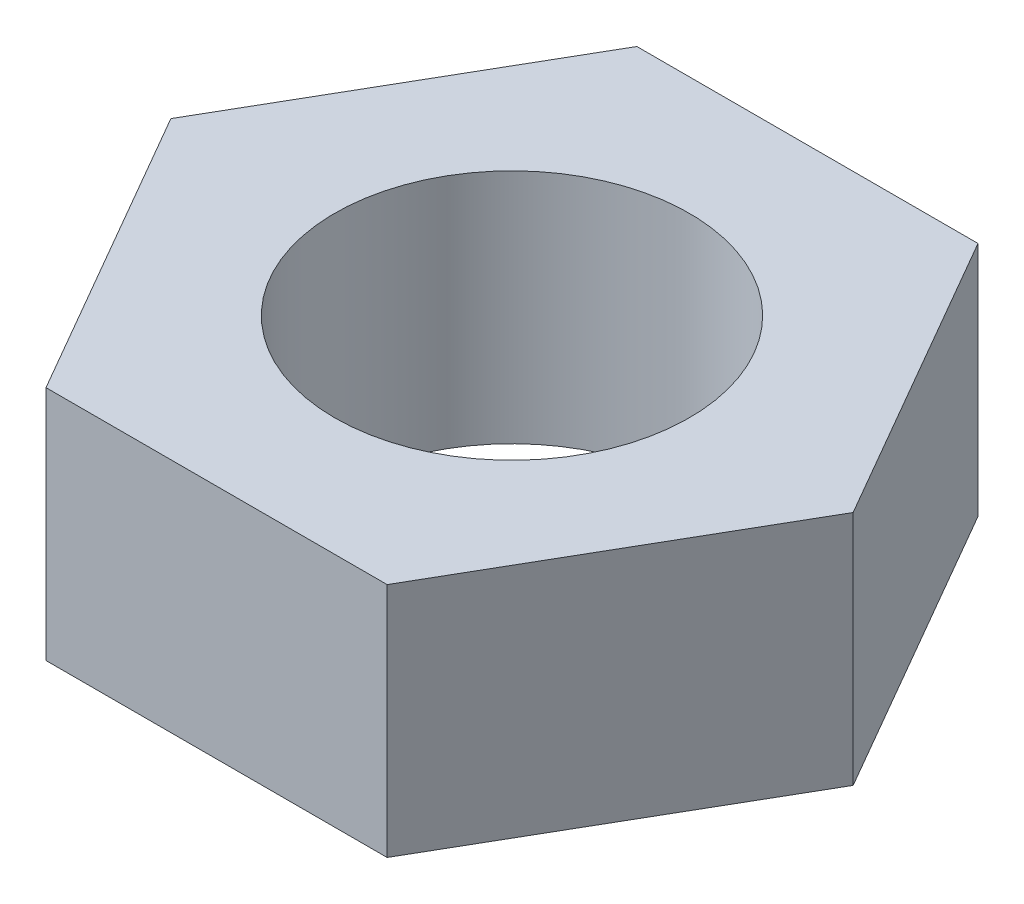
SolidWorks part; units mm, degrees
ref_plane "Front Plane" through (0, 0, 0) normal (0, 0, 1) x (1, 0, 0)
ref_plane "Top Plane" through (0, 0, 0) normal (0, 1, 0) x (1, 0, 0)
ref_plane "Right Plane" through (0, 0, 0) normal (1, 0, 0) x (0, 0, -1)
sketch "Sketch1" plane through (0, 0, 0) normal (0, 1, 0) x (1, 0, 0)
  line L7 (2.1651, 3.75) -> (-2.1651, 3.75)
  line L8 (-2.1651, 3.75) -> (-4.3301, 0)
  line L9 (-4.3301, 0) -> (-2.1651, -3.75)
  line L10 (-2.1651, -3.75) -> (2.1651, -3.75)
  line L11 (2.1651, -3.75) -> (4.3301, 0)
  line L12 (4.3301, 0) -> (2.1651, 3.75)
  circle A0 centre (0, 0) radius 3.75 construction
  circle A1 centre (0, 0) radius 2.25
  point P11 (0, 0)
  dimension "D2" = 4.5
  dimension "D1" = 7.5
extrude "Boss-Extrude1" add sketch "Sketch1" along normal blind 3
